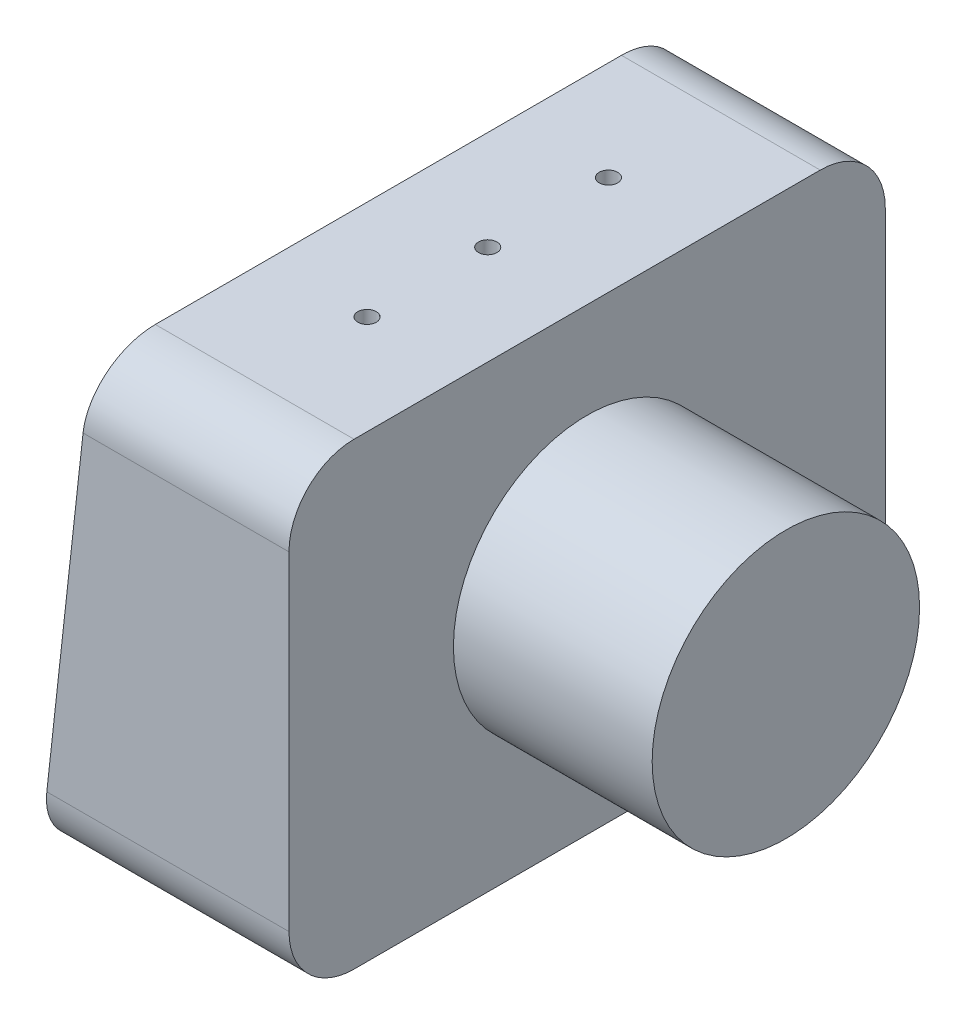
SolidWorks part; units mm, degrees
material "BM"
ref_plane "Спереди" through (0, 0, 0) normal (0, 0, 1) x (1, 0, 0)
ref_plane "Сверху" through (0, 0, 0) normal (0, 1, 0) x (1, 0, 0)
ref_plane "Справа" through (0, 0, 0) normal (1, 0, 0) x (0, 0, -1)
sketch "Эскиз1" plane through (0, 0, 0) normal (0, 0, 1) x (1, 0, 0)
  line L0 (0, 0) -> (0, 127)
  line L1 (0, 127) -> (-55, 127)
  line L2 (-55, 127) -> (-69, 0)
  line L3 (-69, 0) -> (0, 0)
  dimension "D1" = 127
  dimension "D2" = 55
  dimension "D3" = 69
extrude "Бобышка-Вытянуть1" add sketch "Эскиз1" along normal blind 165
fillet "Скругление1" radius 18 4 edges at (-34.5, 0, 165) (-34.5, 0, 0) (-27.5, 127, 0) (-27.5, 127, 165)
sketch "Эскиз2" plane through (0, 0, 0) normal (1, 0, 0) x (0, 0, -1)
  line L0 (-82.5, 127) -> (-82.5, 0) construction
  line L1 (-147, 127) -> (-18, 127) construction
  line L2 (-147, 0) -> (-18, 0) construction
  circle A0 centre (-82.5, 63.5) radius 37
  dimension "D1" = 74
extrude "Бобышка-Вытянуть2" add sketch "Эскиз2" along normal blind 55
sketch "Эскиз3" plane through (0, 127, 0) normal (0, 1, 0) x (1, 0, 0)
  line L0 (-27.5, -18) -> (-27.5, -147) construction
  line L1 (0, -18) -> (-55, -18) construction
  line L2 (-55, -147) -> (0, -147) construction
  point P6 (-27.5, -82.5)
  point P7 (-27.5, -49.1)
  point P8 (-27.5, -115.9)
  dimension "D1" = 33.4
  dimension "D2" = 33.4
hole_wizard "Отверстие обработанное метчиком 1/4-201" positions "Эскиз5" profile "Эскиз4" tap size "1/4-20" standard "Ansi Inch"
sketch "Эскиз5" plane through (0, 127, 0) normal (0, 1, 0) x (1, 0, 0)
  point P0 (-27.5, -49.1)
  point P3 (-27.5, -82.5)
  point P6 (-27.5, -115.9)
sketch "Эскиз4" plane through (-27.5, 127, 49.1) normal (1, 0, 0) x (0, 0, 1)
  line L0 (0, 0) -> (0, 13.5338)
  line L1 (0, 13.5338) -> (2.5527, 12)
  line L2 (2.5527, 12) -> (2.5527, 0)
  line L5 (2.5527, 0) -> (0, 0)
  line L10 (0, 13.5338) -> (-2.5527, 12) construction
  line L11 (0, -6.35) -> (0, 107.95) construction
  dimension "Диаметр сверла" = 5.1054
  dimension "Глубина сверла" = 12
  dimension "Угол заточки сверла" = 118
cosmetic thread "Отверстие резьбы1" parameters "D1"=11, "D2"=6.35
cosmetic thread "Отверстие резьбы2" parameters "D1"=11, "D2"=6.35
cosmetic thread "Отверстие резьбы3" parameters "D1"=11, "D2"=6.35
sketch "Эскиз6" plane through (0, 0, 0) normal (0, -1, 0) x (1, 0, 0)
  line L0 (-34.5, 18) -> (-34.5, 147) construction
  line L1 (-69, 18) -> (0, 18) construction
  line L2 (0, 147) -> (-69, 147) construction
  point P6 (-34.5, 82.5)
hole_wizard "Отверстие обработанное метчиком 1/4-202" positions "Эскиз8" profile "Эскиз7" tap size "1/4-20" standard "Ansi Inch"
sketch "Эскиз8" plane through (0, 0, 0) normal (0, -1, 0) x (-1, 0, 0)
  point P0 (34.5, -82.5)
sketch "Эскиз7" plane through (-34.5, 0, 82.5) normal (1, 0, 0) x (0, 0, -1)
  line L0 (0, 0) -> (0, 13.5338)
  line L1 (0, 13.5338) -> (2.5527, 12)
  line L2 (2.5527, 12) -> (2.5527, 0)
  line L5 (2.5527, 0) -> (0, 0)
  line L10 (0, 13.5338) -> (-2.5527, 12) construction
  line L11 (0, -6.35) -> (0, 107.95) construction
  dimension "Диаметр сверла" = 5.1054
  dimension "Глубина сверла" = 12
  dimension "Угол заточки сверла" = 118
cosmetic thread "Отверстие резьбы4" parameters "D1"=11, "D2"=6.35
sketch "Эскиз9" plane through (-68.1716, 7.515, 0) normal (-0.994, 0.1096, 0) x (0, 0, 1)
  line L8 (18, -1.5605) -> (147, -1.5605)
  line L9 (159, 10.5485) -> (159, 102.0998)
  line L10 (147, 114.2088) -> (18, 114.2088)
  line L11 (6, 102.0998) -> (6, 10.5485)
  line L12 (18, -1.5605) -> (147, -1.5605)
  line L13 (159, 10.5485) -> (159, 102.0998)
  line L14 (147, 114.2088) -> (18, 114.2088)
  line L15 (6, 102.0998) -> (6, 10.5485)
  spline S0 degree 3 poles (-724.6659, 3899.1456) (-83.6914, 549.7421) (82.1476, -14.8565) (149.7327, -1.249) (150.1142, -1.1524) (150.8706, -0.9202) (151.2461, -0.7841) (152.3378, -0.3257) (153.0278, 0.0481) (154.0067, 0.7101) (154.325, 0.949) (154.9351, 1.4562) (155.2254, 1.723) (156.0534, 2.5617) (156.5487, 3.1716) (157.2043, 4.1644) (157.407, 4.507) (157.7749, 5.2038) (158.1073, 5.9153) (158.3698, 6.656) (158.5969, 7.4115) (158.693, 7.7985) (176.2628, 96.984) (-799.8646, 299.5662) (-3771.584, 730.6762) knots -10.790757 -10.790757 -10.790757 -10.790757 0.125 0.125 0.1875 0.1875 0.25 0.25 0.375 0.375 0.4375 0.4375 0.5 0.5 0.625 0.625 0.6875 0.6875 0.75 0.8125 0.8125 0.875 0.875 15.137891 15.137891 15.137891 15.137891 only from (147, -1.5605) to (159, 10.5485)
  spline S1 degree 3 poles (-3741.2666, -771.3546) (-401.5328, -132.6673) (172.2239, 35.8035) (158.6966, 104.8338) (158.6025, 105.2158) (158.3762, 105.9732) (158.2433, 106.35) (157.7951, 107.4471) (157.4291, 108.1412) (156.564, 109.4557) (156.0595, 110.0797) (154.9555, 111.1996) (154.3528, 111.7024) (153.3711, 112.3689) (153.0298, 112.5766) (152.3358, 112.9532) (151.6271, 113.2933) (150.8894, 113.562) (150.1371, 113.7945) (149.7523, 113.8928) (57.4568, 132.5974) (-152.3577, -944.3722) (-555.6972, -3819.5589) knots -11.015346 -11.015346 -11.015346 -11.015346 0.125 0.125 0.1875 0.1875 0.25 0.25 0.375 0.375 0.5 0.5 0.625 0.625 0.6875 0.6875 0.75 0.8125 0.8125 0.875 0.875 15.620441 15.620441 15.620441 15.620441 only from (159, 102.0998) to (147, 114.2088)
  spline S2 degree 3 poles (889.6659, -3786.4973) (248.6914, -437.0938) (82.8524, 127.5048) (15.2673, 113.8973) (14.8858, 113.8007) (14.1294, 113.5685) (13.7539, 113.4324) (12.6622, 112.974) (11.9722, 112.6002) (10.9933, 111.9382) (10.675, 111.6993) (10.0649, 111.1921) (9.7746, 110.9254) (8.9466, 110.0866) (8.4513, 109.4767) (7.7957, 108.4839) (7.593, 108.1413) (7.2251, 107.4445) (6.8927, 106.733) (6.6302, 105.9923) (6.4031, 105.2368) (6.307, 104.8498) (-11.2628, 15.6643) (964.8646, -186.9179) (3936.584, -618.0279) knots -10.790757 -10.790757 -10.790757 -10.790757 0.125 0.125 0.1875 0.1875 0.25 0.25 0.375 0.375 0.4375 0.4375 0.5 0.5 0.625 0.625 0.6875 0.6875 0.75 0.8125 0.8125 0.875 0.875 15.137891 15.137891 15.137891 15.137891 only from (18, 114.2088) to (6, 102.0998)
  spline S3 degree 3 poles (3906.2666, 884.003) (566.5328, 245.3156) (-7.2239, 76.8449) (6.3034, 7.8145) (6.3975, 7.4325) (6.6238, 6.6751) (6.7567, 6.2983) (7.2049, 5.2013) (7.5709, 4.5071) (8.436, 3.1926) (8.9405, 2.5686) (10.0445, 1.4487) (10.6472, 0.9459) (11.6289, 0.2794) (11.9702, 0.0717) (12.6642, -0.3048) (13.3729, -0.645) (14.1106, -0.9137) (14.8629, -1.1461) (15.2477, -1.2445) (107.5432, -19.9491) (317.3577, 1057.0206) (720.6972, 3932.2072) knots -11.015346 -11.015346 -11.015346 -11.015346 0.125 0.125 0.1875 0.1875 0.25 0.25 0.375 0.375 0.5 0.5 0.625 0.625 0.6875 0.6875 0.75 0.8125 0.8125 0.875 0.875 15.620441 15.620441 15.620441 15.620441 only from (6, 10.5485) to (18, -1.5605)
  spline S4 degree 3 poles (147, -1.5605) (147.796, -1.5605) (148.5784, -1.4814) (149.7327, -1.249) (150.1142, -1.1524) (150.8706, -0.9202) (151.2461, -0.7841) (152.3378, -0.3257) (153.0278, 0.0481) (154.0067, 0.7101) (154.325, 0.949) (154.9351, 1.4562) (155.2254, 1.723) (156.0534, 2.5617) (156.5487, 3.1716) (157.2043, 4.1644) (157.407, 4.507) (157.7749, 5.2038) (158.1073, 5.9153) (158.3698, 6.656) (158.5969, 7.4115) (158.693, 7.7985) (158.923, 8.9658) (159, 9.7528) (159, 10.5485) knots 0 0 0 0 0.125 0.125 0.1875 0.1875 0.25 0.25 0.375 0.375 0.4375 0.4375 0.5 0.5 0.625 0.625 0.6875 0.6875 0.75 0.8125 0.8125 0.875 0.875 1 1 1 1
  spline S5 degree 3 poles (159, 102.0998) (159, 102.8957) (158.923, 103.6785) (158.6966, 104.8338) (158.6025, 105.2158) (158.3762, 105.9732) (158.2433, 106.35) (157.7951, 107.4471) (157.4291, 108.1412) (156.564, 109.4557) (156.0595, 110.0797) (154.9555, 111.1996) (154.3528, 111.7024) (153.3711, 112.3689) (153.0298, 112.5766) (152.3358, 112.9532) (151.6271, 113.2933) (150.8894, 113.562) (150.1371, 113.7945) (149.7523, 113.8928) (148.5837, 114.1297) (147.7961, 114.2088) (147, 114.2088) knots 0 0 0 0 0.125 0.125 0.1875 0.1875 0.25 0.25 0.375 0.375 0.5 0.5 0.625 0.625 0.6875 0.6875 0.75 0.8125 0.8125 0.875 0.875 1 1 1 1
  spline S6 degree 3 poles (18, 114.2088) (17.204, 114.2088) (16.4216, 114.1297) (15.2673, 113.8973) (14.8858, 113.8007) (14.1294, 113.5685) (13.7539, 113.4324) (12.6622, 112.974) (11.9722, 112.6002) (10.9933, 111.9382) (10.675, 111.6993) (10.0649, 111.1921) (9.7746, 110.9254) (8.9466, 110.0866) (8.4513, 109.4767) (7.7957, 108.4839) (7.593, 108.1413) (7.2251, 107.4445) (6.8927, 106.733) (6.6302, 105.9923) (6.4031, 105.2368) (6.307, 104.8498) (6.077, 103.6825) (6, 102.8956) (6, 102.0998) knots 0 0 0 0 0.125 0.125 0.1875 0.1875 0.25 0.25 0.375 0.375 0.4375 0.4375 0.5 0.5 0.625 0.625 0.6875 0.6875 0.75 0.8125 0.8125 0.875 0.875 1 1 1 1
  spline S7 degree 3 poles (6, 10.5485) (6, 9.7526) (6.077, 8.9698) (6.3034, 7.8145) (6.3975, 7.4325) (6.6238, 6.6751) (6.7567, 6.2983) (7.2049, 5.2013) (7.5709, 4.5071) (8.436, 3.1926) (8.9405, 2.5686) (10.0445, 1.4487) (10.6472, 0.9459) (11.6289, 0.2794) (11.9702, 0.0717) (12.6642, -0.3048) (13.3729, -0.645) (14.1106, -0.9137) (14.8629, -1.1461) (15.2477, -1.2445) (16.4163, -1.4813) (17.2039, -1.5605) (18, -1.5605) knots 0 0 0 0 0.125 0.125 0.1875 0.1875 0.25 0.25 0.375 0.375 0.5 0.5 0.625 0.625 0.6875 0.6875 0.75 0.8125 0.8125 0.875 0.875 1 1 1 1
  dimension "D1" = 6
extrude "Бобышка-Вытянуть3" add sketch "Эскиз9" along normal blind 1
sketch "Эскиз10" plane through (-69.1656, 7.6245, 0) normal (-0.994, 0.1096, 0) x (0, 0, 1)
  line L0 (82.5, 114.2088) -> (82.5, -1.5605) construction
  line L1 (147, 114.2088) -> (18, 114.2088) construction
  line L2 (18, -1.5605) -> (147, -1.5605) construction
  line L4 (21.5492, 95.8881) -> (143.4508, 95.8881)
  line L5 (21.5492, 95.8881) -> (21.5492, 16.7602)
  line L6 (21.5492, 16.7602) -> (143.4508, 16.7602)
  line L7 (143.4508, 95.8881) -> (143.4508, 16.7602)
  line L8 (21.5492, 95.8881) -> (143.4508, 16.7602) construction
  line L9 (21.5492, 16.7602) -> (143.4508, 95.8881) construction
  point P6 (82.5, 56.3242)
  dimension "D1" = 79.1279
  dimension "D2" = 121.9016
extrude "Вырез-Вытянуть1" cut sketch "Эскиз10" against normal blind 0.5 flip side to cut
equation "\"D2@Эскиз3\"=\"D1@Эскиз3\""
